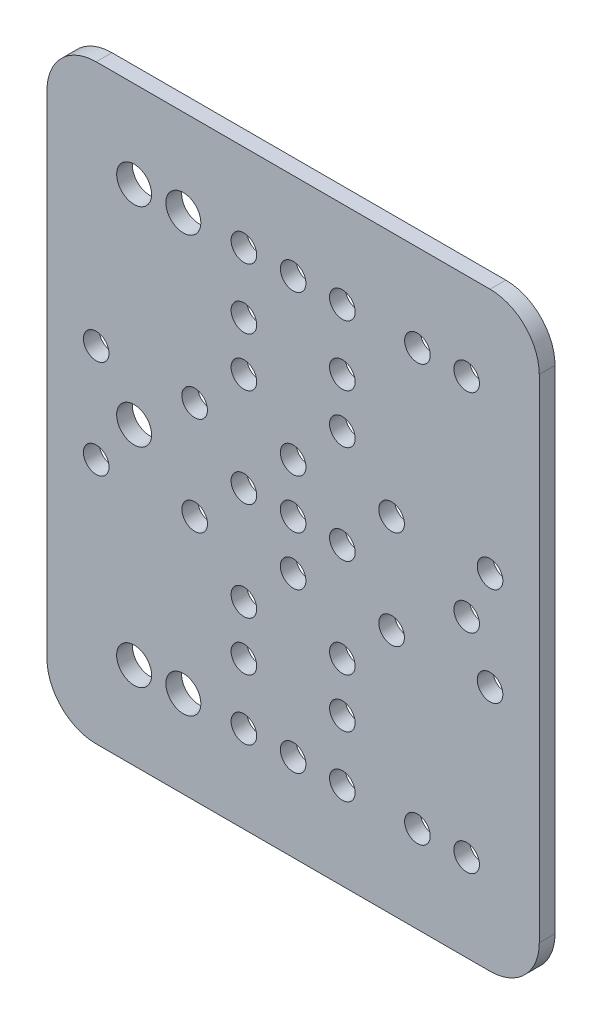
SolidWorks part; units mm, degrees
ref_plane "Front Plane" through (0, 0, 0) normal (0, 0, 1) x (1, 0, 0)
ref_plane "Top Plane" through (0, 0, 0) normal (0, 1, 0) x (1, 0, 0)
ref_plane "Right Plane" through (0, 0, 0) normal (1, 0, 0) x (0, 0, -1)
sketch "Sketch1" plane through (0, 0, 0) normal (0, 0, 1) x (1, 0, 0)
  line L0 (0, 60) -> (0, -60) construction
  line L1 (-50, 60) -> (50, 60)
  line L2 (-50, 60) -> (-50, -60)
  line L3 (-50, -60) -> (50, -60)
  line L4 (50, 60) -> (50, -60)
  line L5 (-50, 60) -> (50, -60) construction
  line L6 (-50, -60) -> (50, 60) construction
  line L7 (-50, 0) -> (50, 0) construction
  circle A0 centre (0, 0) radius 2.6
  circle A1 centre (0, 10) radius 2.6
  circle A2 centre (0, 42.3) radius 2.6
  circle A3 centre (0, -10) radius 2.6
  circle A4 centre (10, -20) radius 2.6
  circle A5 centre (10, 0) radius 2.6
  circle A6 centre (-10, 0) radius 2.6
  circle A7 centre (-32.3, 0) radius 3.55
  circle A8 centre (35.25, 0) radius 2.6
  circle A9 centre (35.25, 42.3) radius 2.6
  circle A10 centre (10, -30) radius 2.6
  circle A11 centre (-10, -20) radius 2.6
  circle A12 centre (-32.3, 42.3) radius 3.55
  circle A13 centre (-22.3, 42.3) radius 3.55
  circle A14 centre (-10, -30) radius 2.6
  circle A15 centre (-40, 10) radius 2.6
  circle A16 centre (-20, 10) radius 2.6
  circle A17 centre (20, 10) radius 2.6
  circle A18 centre (40, 10) radius 2.6
  circle A19 centre (40, -10) radius 2.6
  circle A20 centre (20, -10) radius 2.6
  circle A21 centre (-20, -10) radius 2.6
  circle A22 centre (-40, -10) radius 2.6
  circle A23 centre (25.25, 42.3) radius 2.6
  circle A24 centre (10, 42.3) radius 2.6
  circle A25 centre (-10, 42.3) radius 2.6
  circle A26 centre (-10, 30) radius 2.6
  circle A27 centre (-10, 20) radius 2.6
  circle A28 centre (10, 30) radius 2.6
  circle A29 centre (10, 20) radius 2.6
  circle A30 centre (-10, -42.3) radius 2.6
  circle A31 centre (10, -42.3) radius 2.6
  circle A32 centre (25.25, -42.3) radius 2.6
  circle A33 centre (-22.3, -42.3) radius 3.55
  circle A34 centre (-32.3, -42.3) radius 3.55
  circle A35 centre (35.25, -42.3) radius 2.6
  circle A36 centre (0, -42.3) radius 2.6
  point P0 (0, 0)
  dimension "D3" = 7.1
  dimension "D4" = 5.2
  dimension "D1" = 100
  dimension "D2" = 120
  dimension "D5" = 10
  dimension "D6" = 10
  dimension "D7" = 2
  dimension "D9" = 10
  dimension "D10" = 32.3
  dimension "D11" = 10
  dimension "D12" = 40
  dimension "D13" = 20
  dimension "D14" = 20
  dimension "D15" = 40
  dimension "D16" = 10
  dimension "D17" = 12.3
  dimension "D18" = 10
  dimension "D19" = 17.7
  dimension "D20" = 10
extrude "Boss-Extrude1" add sketch "Sketch1" along normal blind 3.2
fillet "Fillet1" radius 10 4 edges at (-50, -60, 1.6) (50, -60, 1.6) (50, 60, 1.6) (-50, 60, 1.6)
